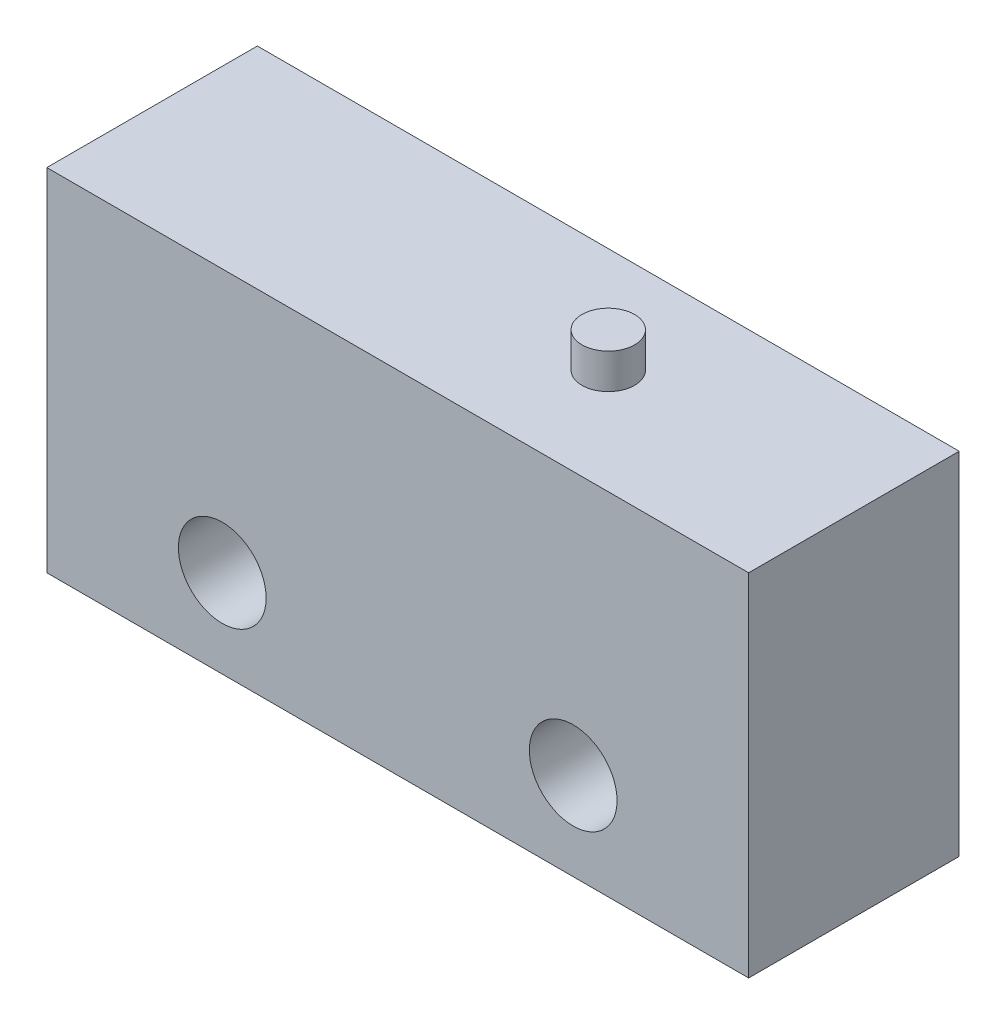
SolidWorks part; units mm, degrees
ref_plane "Front Plane" through (0, 0, 0) normal (0, 0, 1) x (1, 0, 0)
ref_plane "Top Plane" through (0, 0, 0) normal (0, 1, 0) x (1, 0, 0)
ref_plane "Right Plane" through (0, 0, 0) normal (1, 0, 0) x (0, 0, -1)
sketch "Sketch1" plane through (0, 0, 0) normal (0, 0, 1) x (1, 0, 0)
  line L1 (10, -5) -> (-10, -5)
  line L2 (10, -5) -> (10, 5)
  line L3 (10, 5) -> (-10, 5)
  line L4 (-10, -5) -> (-10, 5)
  line L5 (10, -5) -> (-10, 5) construction
  line L6 (10, 5) -> (-10, -5) construction
  circle A0 centre (-5, -2.5) radius 1.25
  circle A1 centre (5, -2.5) radius 1.25
  point P0 (0, 0)
  dimension "D3" = 2.5
  dimension "D4" = 2.5
  dimension "D5" = 2.5
  dimension "D6" = 2.5
  dimension "D7" = 5
  dimension "D8" = 5
  dimension "D1" = 20
  dimension "D2" = 10
extrude "Boss-Extrude1" add sketch "Sketch1" along normal blind 6 contours A0 | A1 | L4 L3 L2 L1
sketch "Sketch2" plane through (0, 5, 0) normal (0, 1, 0) x (1, 0, 0)
  line L0 (10, -6) -> (10, 0) construction
  circle A0 centre (3, -3) radius 0.75
  dimension "D1" = 1.5
  dimension "D2" = 7
extrude "Boss-Extrude2" add sketch "Sketch2" along normal blind 1
